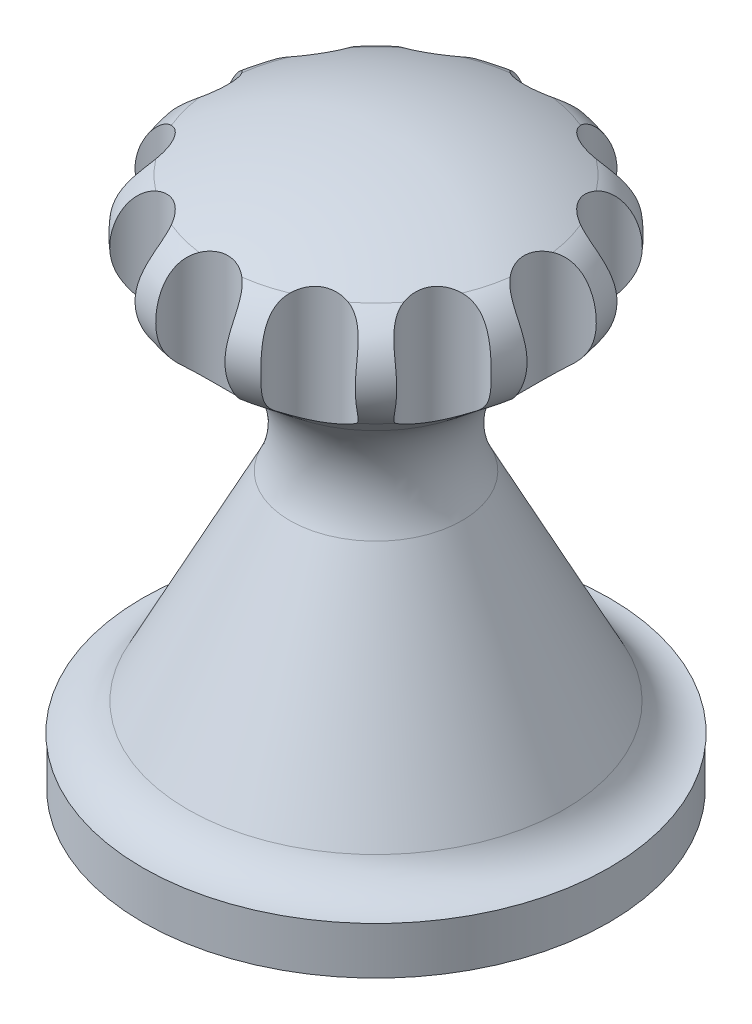
SolidWorks part; units mm, degrees
material "7075-T6, Plate (SS)"
ref_plane "Ebene vorne" through (0, 0, 0) normal (0, 0, 1) x (1, 0, 0)
ref_plane "Ebene oben" through (0, 0, 0) normal (0, 1, 0) x (1, 0, 0)
ref_plane "Ebene rechts" through (0, 0, 0) normal (1, 0, 0) x (0, 0, -1)
sketch "Skizze1" plane through (0, 0, 0) normal (0, 0, 1) x (1, 0, 0)
  line L0 (0, 617.4734) -> (0, 0) construction
  line L1 (0, 0) -> (-253.1172, 0)
  line L2 (-253.1172, 0) -> (-253.1172, 51.793)
  line L3 (-253.1172, 51.793) -> (-253.6474, 51.793)
  line L4 (-204.4573, 81.8663) -> (-93.6048, 298.3102)
  line L5 (-119.3338, 420.4096) -> (-181.8088, 471.1488)
  line L6 (0, 617.4734) -> (0, 0)
  arc A0 (-253.6474, 51.793) -> (-204.4573, 81.8663) centre (-253.6474, 107.0592) ccw
  arc A1 (-93.6048, 298.3102) -> (-119.3338, 420.4096) centre (-181.8088, 343.4842) ccw
  arc A2 (-181.8088, 471.1488) -> (-170.5402, 576.6973) centre (-141.9184, 520.2658) cw
  arc A3 (-170.5402, 576.6973) -> (0, 617.4734) centre (0, 240.4557) cw
revolve "Rotation1" add sketch "Skizze1" angle 360 about L6
sketch "Skizze2" plane through (0, 0, 0) normal (0, 0, 1) x (1, 0, 0)
  line L0 (-198.6692, 595.2658) -> (-198.6692, 520.2658) construction
  line L1 (-198.6692, 520.2658) -> (-198.6692, 445.2658) construction
  line L2 (-198.6692, 595.2658) -> (-198.6692, 445.2658)
  line L3 (-198.6692, 595.2658) -> (-236.3897, 595.2658)
  line L4 (-236.3897, 595.2658) -> (-236.3897, 445.2658)
  line L5 (-236.3897, 445.2658) -> (-198.6692, 445.2658)
  line L6 (-198.6692, 520.2658) -> (-141.9184, 520.2658) construction
  dimension "D1" = 150
revolve "Schnitt-Rotation1" cut sketch "Skizze2" angle 360 about L2
pattern_circular "Kreismuster1" count 12 over 360 about axis through (0, 0, 0) along (0, 1, 0) of "Schnitt-Rotation1"
equation "\"LÄNGE\"=0"
equation "\"BREITE\"=0"
equation "\"HÖHE\"=0"
equation "\"DURCHMESSER\"=0"
equation "\"Stückzahl\"= 1"
equation "\"W_ID\"= 0000"
